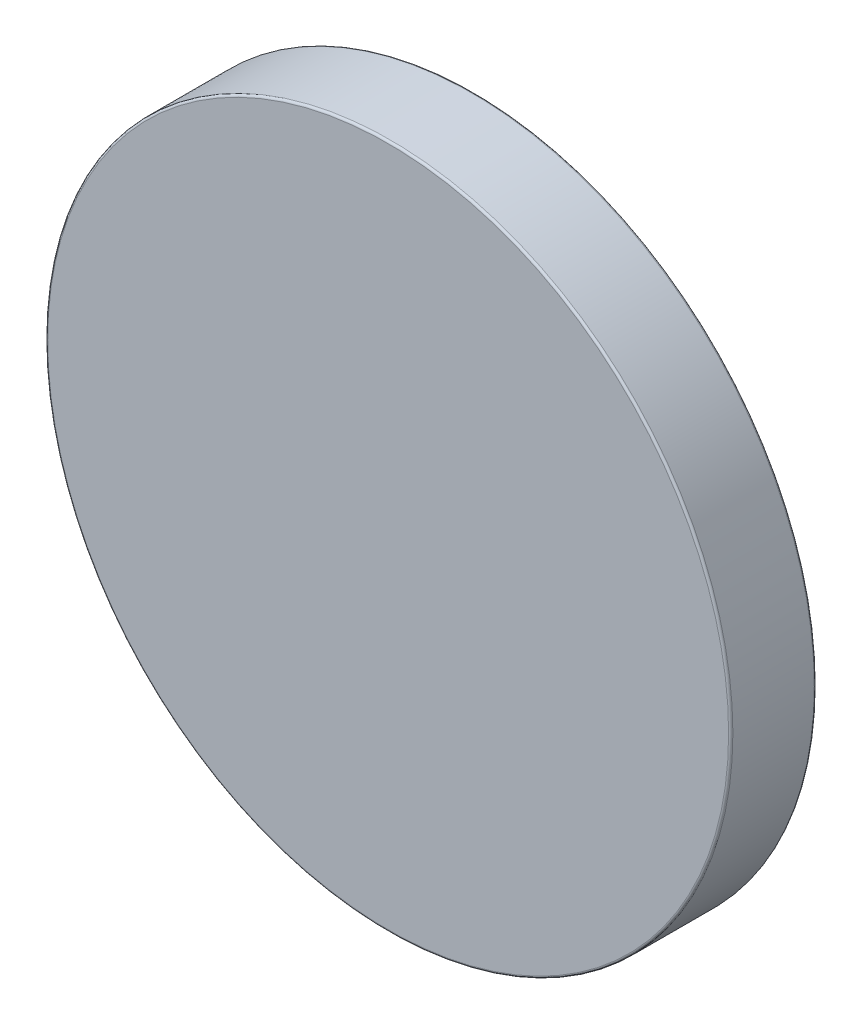
SolidWorks part; units mm, degrees
ref_plane "Front Plane" through (0, 0, 0) normal (0, 0, 1) x (1, 0, 0)
ref_plane "Top Plane" through (0, 0, 0) normal (0, 1, 0) x (1, 0, 0)
ref_plane "Right Plane" through (0, 0, 0) normal (1, 0, 0) x (0, 0, -1)
sketch "Sketch1" plane through (0, 0, 0) normal (0, 0, 1) x (1, 0, 0)
  circle A0 centre (0, 0) radius 12.7 construction
  dimension "OD" = 25.4
sketch "Sketch2" plane through (0, 0, 0) normal (1, 0, 0) x (0, 0, -1)
  line L0 (-1.5875, 0) -> (1.5875, 0) construction
  line L1 (0, 12.7) -> (0, -12.7) construction
  line L3 (-1.5875, 12.7) -> (1.5875, 12.7)
  line L4 (-1.5875, 12.7) -> (-1.5875, -12.7)
  line L5 (-1.5875, -12.7) -> (1.5875, -12.7)
  line L6 (1.5875, 12.7) -> (1.5875, -12.7)
  point P4 (0, 0)
  point P12 (0, 12.7)
  dimension "Thickness" = 3.175
sketch "Sketch3" plane through (0, 0, 0) normal (0, 0, 1) x (1, 0, 0)
  circle A0 centre (0, 0) radius 12.7 construction
  circle A1 centre (0, 0) radius 12.7
extrude "Boss-Extrude1" add sketch "Sketch3" along normal up to vertex (1.5875 mm away) and the other way up to vertex (1.5875 mm away) up to point (0, 12.7, 1.5875) other way up to point (0, 12.7, -1.5875)
fillet "Fillet1" radius 0.0794 2 edges at (12.7, 0, -1.5875) (12.7, 0, 1.5875)
equation "\"Fillet@Fillet1\"=\"Thickness@Sketch2\"*.025"
